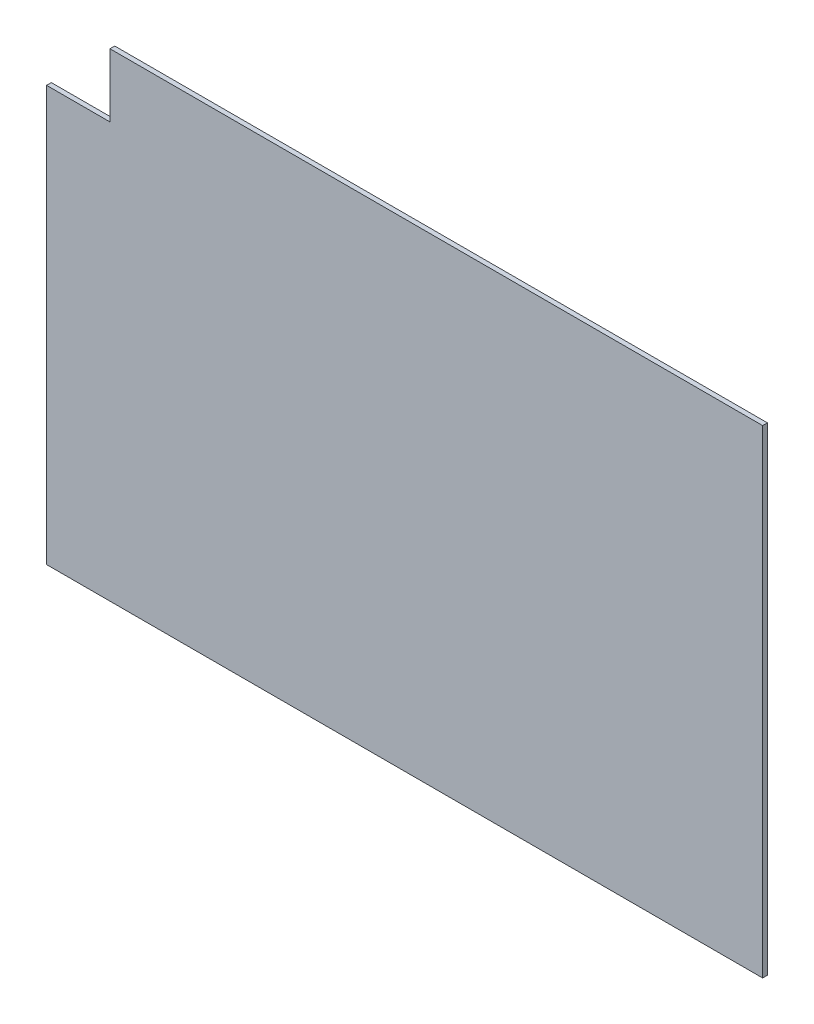
SolidWorks part; units mm, degrees
ref_plane "正面" through (0, 0, 0) normal (0, 0, 1) x (1, 0, 0)
ref_plane "平面" through (0, 0, 0) normal (0, 1, 0) x (1, 0, 0)
ref_plane "右側面" through (0, 0, 0) normal (1, 0, 0) x (0, 0, -1)
sketch "ｽｹｯﾁ1" plane through (0, 0, 0) normal (0, 0, 1) x (1, 0, 0)
  line L0 (0, -1.65) -> (0, 1.65) construction
  line L1 (-226, -152.0762) -> (226, -152.0762)
  line L2 (-226, -152.0762) -> (-226, 149.9238)
  line L3 (-226, 149.9238) -> (226, 149.9238)
  line L4 (226, -152.0762) -> (226, 149.9238)
  line L5 (-226, -152.0762) -> (226, 149.9238) construction
  line L6 (-226, 149.9238) -> (226, -152.0762) construction
  line L7 (-226, 109.9238) -> (-186, 109.9238)
  line L8 (-186, 109.9238) -> (-186, 149.9238)
  point P0 (0, -1.0762)
  dimension "D1" = 302
  dimension "D2" = 452
  dimension "D3" = 40
  dimension "D4" = 40
extrude "ﾎﾞｽ - 押し出し1" add sketch "ｽｹｯﾁ1" along normal mid plane 3 contours L8 L7 L2 L1 L4 L3
